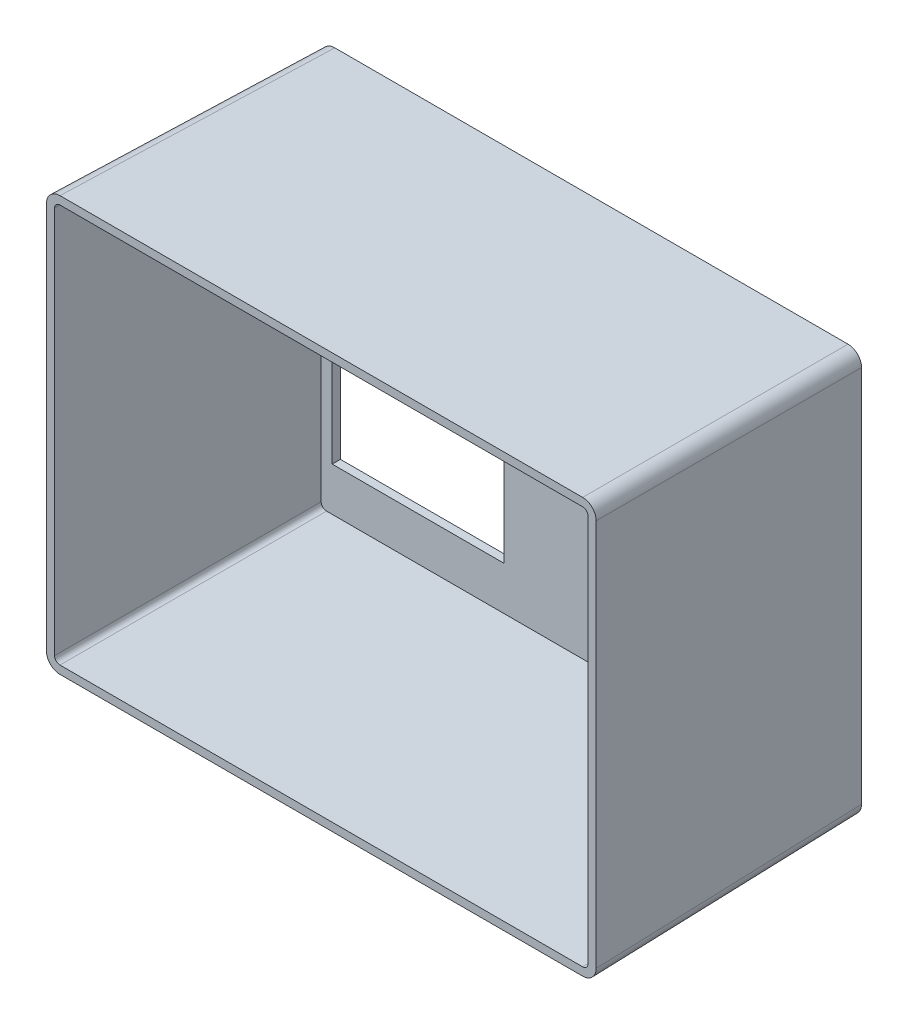
SolidWorks part; units mm, degrees
ref_plane "Front Plane" through (0, 0, 0) normal (0, 0, 1) x (1, 0, 0)
ref_plane "Top Plane" through (0, 0, 0) normal (0, 1, 0) x (1, 0, 0)
ref_plane "Right Plane" through (0, 0, 0) normal (1, 0, 0) x (0, 0, -1)
sketch "Sketch2" plane through (0, 0, 0) normal (0, 0, 1) x (1, 0, 0)
  line L0 (446, 1816) -> (2230, 1816) construction
sketch "Sketch3" plane through (0, 0, 0) normal (0, 0, 1) x (1, 0, 0)
  line L1 (-128.9269, 138.1103) -> (71.0731, 138.1103)
  line L2 (-128.9269, 138.1103) -> (-128.9269, -11.8897)
  line L3 (-128.9269, -11.8897) -> (71.0731, -11.8897)
  line L4 (71.0731, 138.1103) -> (71.0731, -11.8897)
  line L5 (-128.9269, 138.1103) -> (71.0731, -11.8897) construction
  line L6 (-128.9269, -11.8897) -> (71.0731, 138.1103) construction
  point P0 (-28.9269, 63.1103)
  dimension "D1" = 200
  dimension "D2" = 150
extrude "Boss-Extrude1" add sketch "Sketch3" along normal blind 100 draft 1 draft outward yes
fillet "Fillet1" radius 5 4 edges at (71.9458, -12.7624, 50) (-129.7997, 138.9831, 50) (71.9458, 138.9831, 50) (-129.7997, -12.7624, 50)
shell "Shell1" thickness 3
sketch "Sketch10" plane through (0, 0, 0) normal (0, 0, -1) x (-1, 0, 0)
  line L1 (-51.3314, 132.0675) -> (-31.3314, 132.0675)
  line L2 (-51.3314, 132.0675) -> (-51.3314, 106.6675)
  line L3 (-51.3314, 106.6675) -> (-31.3314, 106.6675)
  line L4 (-31.3314, 132.0675) -> (-31.3314, 106.6675)
  line L5 (-51.3314, 132.0675) -> (-31.3314, 106.6675) construction
  line L6 (-51.3314, 106.6675) -> (-31.3314, 132.0675) construction
  line L7 (-63.8252, -2.3278) -> (-13.8252, -2.3278)
  line L8 (-63.8252, -2.3278) -> (-63.8252, 17.6722)
  line L9 (-63.8252, 17.6722) -> (-13.8252, 17.6722)
  line L10 (-13.8252, -2.3278) -> (-13.8252, 17.6722)
  line L11 (-63.8252, -2.3278) -> (-13.8252, 17.6722) construction
  line L12 (-63.8252, 17.6722) -> (-13.8252, -2.3278) construction
  point P0 (-38.8252, 7.6722)
  dimension "D1" = 20
  dimension "D2" = 25.4
  dimension "D3" = 20
  dimension "D4" = 50
extrude "Cut-Extrude6" cut sketch "Sketch10" against normal blind 59.614 draft 1 draft outward yes
sketch "Sketch12" plane through (0, 0, 0) normal (0, 0, -1) x (-1, 0, 0)
  line L1 (58.3418, 45.3254) -> (121.8418, 45.3254)
  line L2 (58.3418, 45.3254) -> (58.3418, 7.2254)
  line L3 (58.3418, 7.2254) -> (121.8418, 7.2254)
  line L4 (121.8418, 45.3254) -> (121.8418, 7.2254)
  line L5 (58.3418, 45.3254) -> (121.8418, 7.2254) construction
  line L6 (58.3418, 7.2254) -> (121.8418, 45.3254) construction
  dimension "D1" = 38.1
  dimension "D2" = 63.5
extrude "Cut-Extrude7" cut sketch "Sketch12" against normal blind 100 draft 1 draft outward yes
